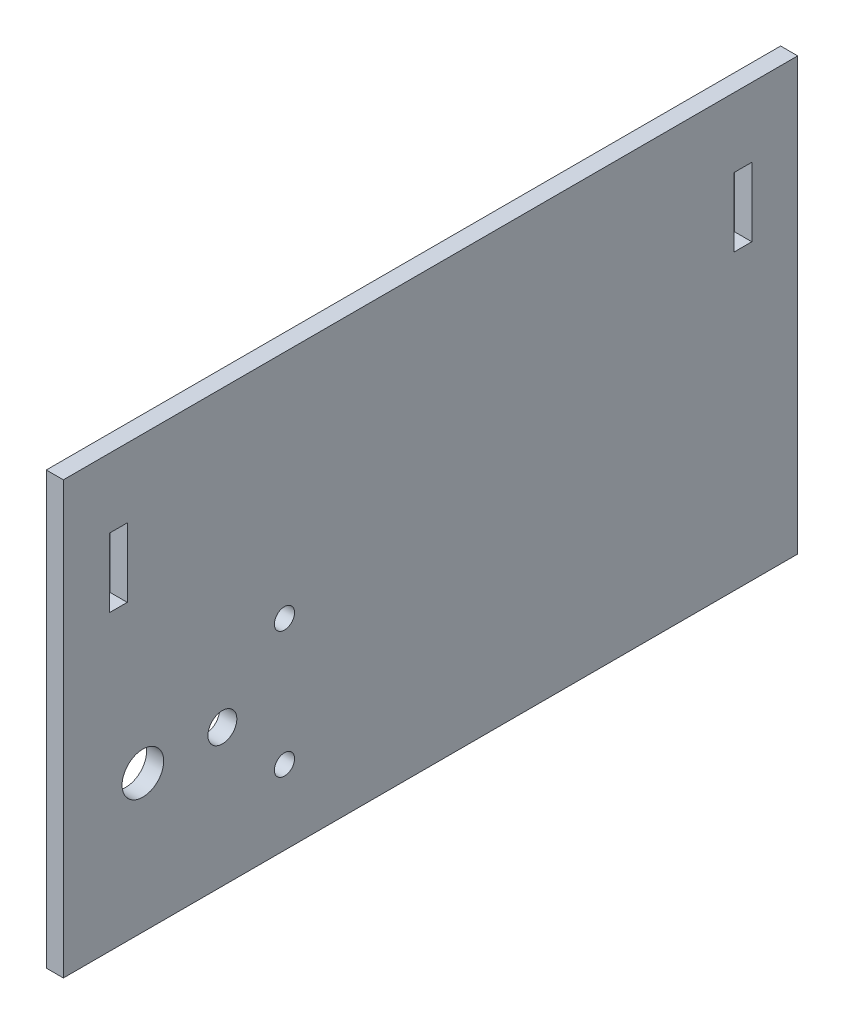
SolidWorks part; units mm, degrees
ref_plane "Front Plane" through (0, 0, 0) normal (0, 0, 1) x (1, 0, 0)
ref_plane "Top Plane" through (0, 0, 0) normal (0, 1, 0) x (1, 0, 0)
ref_plane "Right Plane" through (0, 0, 0) normal (1, 0, 0) x (0, 0, -1)
sketch "Sketch1" plane through (0, 0, 0) normal (1, 0, 0) x (0, 0, -1)
  line L1 (0, 0) -> (101.6, 0)
  line L2 (0, 0) -> (0, 59.69)
  line L3 (0, 59.69) -> (101.6, 59.69)
  line L4 (101.6, 0) -> (101.6, 59.69)
  dimension "D1" = 101.6
  dimension "D2" = 59.69
extrude "Boss-Extrude1" add sketch "Sketch1" along normal blind 2.3622
sketch "Sketch2" plane through (2.3622, 0, 0) normal (1, 0, 0) x (0, 0, -1)
  line L0 (11, 19.05) -> (30.591, 19.05) construction
  line L2 (0, 59.69) -> (0, 0) construction
  line L4 (30.591, 27.8) -> (30.591, 10.3) construction
  line L5 (0, 0) -> (101.6, 0) construction
  circle A4 centre (30.591, 10.3) radius 1.4
  circle A5 centre (30.591, 27.8) radius 1.4
  circle A6 centre (22, 19.05) radius 2
  circle A7 centre (11, 19.05) radius 2.877
  dimension "D2" = 4
  dimension "D3" = 2.8
  dimension "D1" = 5.754
  dimension "D4" = 2.8
  dimension "D8" = 11
  dimension "D5" = 11
  dimension "D6" = 19.591
  dimension "D7" = 19.05
  dimension "D10" = 17.5
  dimension "D11" = 8.75
extrude "Cut-Extrude1" cut sketch "Sketch2" against normal up to next
sketch "Sketch4" plane through (2.3622, 0, 0) normal (1, 0, 0) x (0, 0, -1)
  line L1 (6.35, 50.1142) -> (8.8392, 50.1142)
  line L2 (6.35, 50.1142) -> (6.35, 40.5892)
  line L3 (6.35, 40.5892) -> (8.8392, 40.5892)
  line L4 (8.8392, 50.1142) -> (8.8392, 40.5892)
  line L6 (50.8, 0) -> (50.8, 53.7349) construction
  line L8 (92.7608, 50.1142) -> (92.7608, 40.5892)
  line L9 (95.25, 40.5892) -> (92.7608, 40.5892)
  line L10 (95.25, 50.1142) -> (95.25, 40.5892)
  line L11 (95.25, 50.1142) -> (92.7608, 50.1142)
  line L17 (0, 59.69) -> (0, 0) construction
  line L18 (101.6, 59.69) -> (0, 59.69) construction
  line L19 (0, 0) -> (101.6, 0) construction
  dimension "D1" = 2.4892
  dimension "D2" = 9.525
  dimension "D3" = 6.35
  dimension "D4" = 9.5758
extrude "Cut-Extrude3" cut sketch "Sketch4" against normal through all
